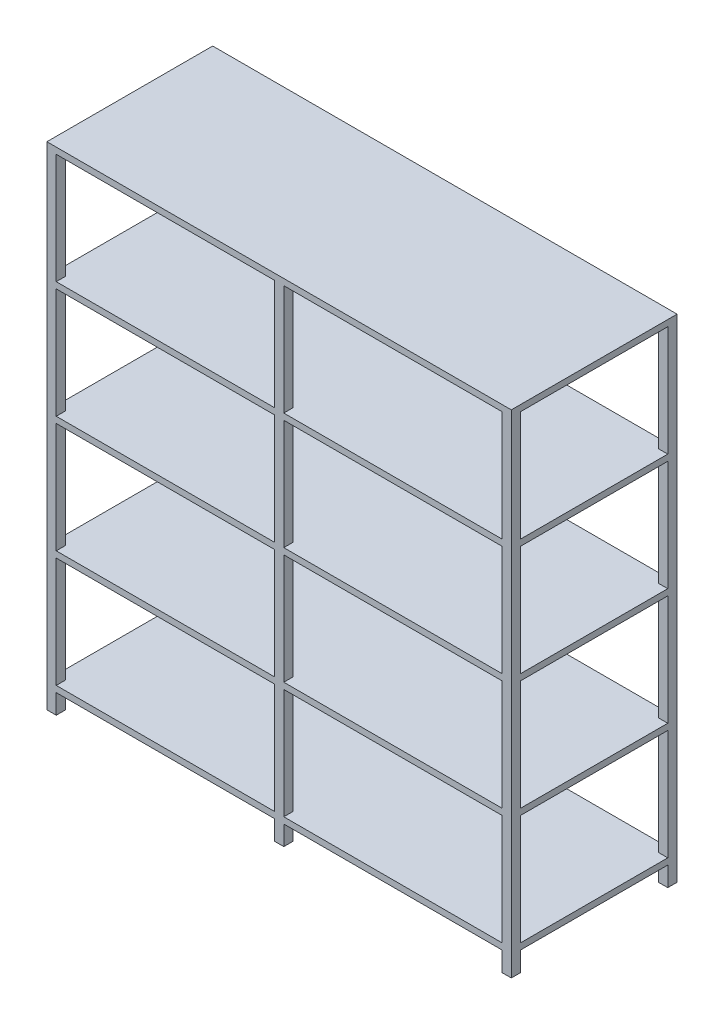
SolidWorks part; units mm, degrees
ref_plane "Alzado" through (0, 0, 0) normal (0, 0, 1) x (1, 0, 0)
ref_plane "Planta" through (0, 0, 0) normal (0, 1, 0) x (1, 0, 0)
ref_plane "Vista lateral" through (0, 0, 0) normal (1, 0, 0) x (0, 0, -1)
sketch "Croquis1" plane through (0, 0, 0) normal (0, 1, 0) x (1, 0, 0)
  line L0 (0, -38.1) -> (0, -338.1) construction
  line L1 (0, 0) -> (38.1, 0)
  line L2 (0, 0) -> (0, -38.1)
  line L3 (0, -38.1) -> (38.1, -38.1)
  line L4 (38.1, 0) -> (38.1, -38.1)
  line L5 (38.1, 0) -> (928.1, 0) construction
  line L6 (966.2, 0) -> (1856.2, 0) construction
  line L7 (928.1, 0) -> (966.2, 0)
  line L8 (928.1, 0) -> (928.1, -38.1)
  line L9 (928.1, -38.1) -> (966.2, -38.1)
  line L10 (966.2, 0) -> (966.2, -38.1)
  line L12 (1856.2, 0) -> (1894.3, 0)
  line L13 (1856.2, 0) -> (1856.2, -38.1)
  line L14 (1856.2, -38.1) -> (1894.3, -38.1)
  line L15 (1894.3, 0) -> (1894.3, -38.1)
  line L16 (0, -338.1) -> (218.5329, -338.1) construction
  line L22 (966.2, -676.2) -> (1856.2, -676.2) construction
  line L23 (38.1, -676.2) -> (928.1, -676.2) construction
  line L28 (1894.3, -676.2) -> (1894.3, -638.1)
  line L29 (1856.2, -638.1) -> (1894.3, -638.1)
  line L30 (1856.2, -676.2) -> (1856.2, -638.1)
  line L31 (1856.2, -676.2) -> (1894.3, -676.2)
  line L32 (966.2, -676.2) -> (966.2, -638.1)
  line L33 (928.1, -638.1) -> (966.2, -638.1)
  line L34 (928.1, -676.2) -> (928.1, -638.1)
  line L35 (928.1, -676.2) -> (966.2, -676.2)
  line L36 (38.1, -676.2) -> (38.1, -638.1)
  line L37 (0, -638.1) -> (38.1, -638.1)
  line L38 (0, -676.2) -> (0, -638.1)
  line L39 (0, -676.2) -> (38.1, -676.2)
  dimension "D1" = 38.1
  dimension "D2" = 38.1
  dimension "D3" = 300
  dimension "D4" = 890
  dimension "D5" = 38.1
  dimension "D6" = 38.1
  dimension "D7" = 890
  dimension "D8" = 38.1
  dimension "D9" = 38.1
extrude "Saliente-Extruir1" add sketch "Croquis1" along normal blind 80
sketch "Croquis2" plane through (0, 80, 0) normal (0, 1, 0) x (1, 0, 0)
  line L1 (0, 0) -> (1894.3, 0)
  line L2 (0, 0) -> (0, -676.2)
  line L3 (0, -676.2) -> (1894.3, -676.2)
  line L4 (1894.3, 0) -> (1894.3, -676.2)
extrude "Saliente-Extruir2" add sketch "Croquis2" along normal blind 25.4
sketch "Croquis3" plane through (0, 105.4, 0) normal (0, 1, 0) x (1, 0, 0)
  line L1 (38.1, -38.1) -> (0, -38.1)
  line L2 (38.1, -38.1) -> (38.1, 0)
  line L3 (38.1, 0) -> (0, 0)
  line L4 (0, -38.1) -> (0, 0)
  line L5 (928.1, 0) -> (966.2, 0)
  line L6 (928.1, 0) -> (928.1, -38.1)
  line L7 (928.1, -38.1) -> (966.2, -38.1)
  line L8 (966.2, 0) -> (966.2, -38.1)
  line L9 (1856.2, 0) -> (1894.3, 0)
  line L10 (1856.2, 0) -> (1856.2, -38.1)
  line L11 (1856.2, -38.1) -> (1894.3, -38.1)
  line L12 (1894.3, 0) -> (1894.3, -38.1)
  line L13 (1856.2, -638.1) -> (1894.3, -638.1)
  line L14 (1856.2, -638.1) -> (1856.2, -676.2)
  line L15 (1856.2, -676.2) -> (1894.3, -676.2)
  line L16 (1894.3, -638.1) -> (1894.3, -676.2)
  line L17 (928.1, -638.1) -> (966.2, -638.1)
  line L18 (928.1, -638.1) -> (928.1, -676.2)
  line L19 (928.1, -676.2) -> (966.2, -676.2)
  line L20 (966.2, -638.1) -> (966.2, -676.2)
  line L21 (0, -638.1) -> (38.1, -638.1)
  line L22 (0, -638.1) -> (0, -676.2)
  line L23 (0, -676.2) -> (38.1, -676.2)
  line L24 (38.1, -638.1) -> (38.1, -676.2)
extrude "Saliente-Extruir3" add sketch "Croquis3" along normal blind 450
sketch "Croquis4" plane through (0, 555.4, 0) normal (0, 1, 0) x (1, 0, 0)
  line L1 (0, 0) -> (1894.3, 0)
  line L2 (0, 0) -> (0, -676.2)
  line L3 (0, -676.2) -> (1894.3, -676.2)
  line L4 (1894.3, 0) -> (1894.3, -676.2)
extrude "Saliente-Extruir4" add sketch "Croquis4" along normal blind 25.4
sketch "Croquis5" plane through (0, 580.8, 0) normal (0, 1, 0) x (1, 0, 0)
  line L1 (38.1, -38.1) -> (0, -38.1)
  line L2 (38.1, -38.1) -> (38.1, 0)
  line L3 (38.1, 0) -> (0, 0)
  line L4 (0, -38.1) -> (0, 0)
  line L5 (928.1, 0) -> (966.2, 0)
  line L6 (928.1, 0) -> (928.1, -38.1)
  line L7 (928.1, -38.1) -> (966.2, -38.1)
  line L8 (966.2, 0) -> (966.2, -38.1)
  line L9 (1856.2, 0) -> (1894.3, 0)
  line L10 (1856.2, 0) -> (1856.2, -38.1)
  line L11 (1856.2, -38.1) -> (1894.3, -38.1)
  line L12 (1894.3, 0) -> (1894.3, -38.1)
  line L13 (1856.2, -638.1) -> (1894.3, -638.1)
  line L14 (1856.2, -638.1) -> (1856.2, -676.2)
  line L15 (1856.2, -676.2) -> (1894.3, -676.2)
  line L16 (1894.3, -638.1) -> (1894.3, -676.2)
  line L17 (928.1, -638.1) -> (966.2, -638.1)
  line L18 (928.1, -638.1) -> (928.1, -676.2)
  line L19 (928.1, -676.2) -> (966.2, -676.2)
  line L20 (966.2, -638.1) -> (966.2, -676.2)
  line L21 (0, -638.1) -> (38.1, -638.1)
  line L22 (0, -638.1) -> (0, -676.2)
  line L23 (0, -676.2) -> (38.1, -676.2)
  line L24 (38.1, -638.1) -> (38.1, -676.2)
extrude "Saliente-Extruir5" add sketch "Croquis5" along normal blind 450
sketch "Croquis6" plane through (0, 1030.8, 0) normal (0, 1, 0) x (1, 0, 0)
  line L1 (0, 0) -> (1894.3, 0)
  line L2 (0, 0) -> (0, -676.2)
  line L3 (0, -676.2) -> (1894.3, -676.2)
  line L4 (1894.3, 0) -> (1894.3, -676.2)
extrude "Saliente-Extruir6" add sketch "Croquis6" along normal blind 25.4
sketch "Croquis7" plane through (0, 1056.2, 0) normal (0, 1, 0) x (1, 0, 0)
  line L1 (38.1, -38.1) -> (0, -38.1)
  line L2 (38.1, -38.1) -> (38.1, 0)
  line L3 (38.1, 0) -> (0, 0)
  line L4 (0, -38.1) -> (0, 0)
  line L5 (928.1, -38.1) -> (966.2, -38.1)
  line L6 (928.1, -38.1) -> (928.1, 0)
  line L7 (928.1, 0) -> (966.2, 0)
  line L8 (966.2, -38.1) -> (966.2, 0)
  line L9 (1856.2, 0) -> (1894.3, 0)
  line L10 (1856.2, 0) -> (1856.2, -38.1)
  line L11 (1856.2, -38.1) -> (1894.3, -38.1)
  line L12 (1894.3, 0) -> (1894.3, -38.1)
  line L13 (1856.2, -638.1) -> (1894.3, -638.1)
  line L14 (1856.2, -638.1) -> (1856.2, -676.2)
  line L15 (1856.2, -676.2) -> (1894.3, -676.2)
  line L16 (1894.3, -638.1) -> (1894.3, -676.2)
  line L17 (928.1, -638.1) -> (966.2, -638.1)
  line L18 (928.1, -638.1) -> (928.1, -676.2)
  line L19 (928.1, -676.2) -> (966.2, -676.2)
  line L20 (966.2, -638.1) -> (966.2, -676.2)
  line L21 (0, -638.1) -> (38.1, -638.1)
  line L22 (0, -638.1) -> (0, -676.2)
  line L23 (0, -676.2) -> (38.1, -676.2)
  line L24 (38.1, -638.1) -> (38.1, -676.2)
extrude "Saliente-Extruir7" add sketch "Croquis7" along normal blind 450
sketch "Croquis8" plane through (0, 1506.2, 0) normal (0, 1, 0) x (1, 0, 0)
  line L1 (0, 0) -> (1894.3, 0)
  line L2 (0, 0) -> (0, -676.2)
  line L3 (0, -676.2) -> (1894.3, -676.2)
  line L4 (1894.3, 0) -> (1894.3, -676.2)
extrude "Saliente-Extruir8" add sketch "Croquis8" along normal blind 25.4
sketch "Croquis9" plane through (0, 1531.6, 0) normal (0, 1, 0) x (1, 0, 0)
  line L1 (0, 0) -> (38.1, 0)
  line L2 (0, 0) -> (0, -38.1)
  line L3 (0, -38.1) -> (38.1, -38.1)
  line L4 (38.1, 0) -> (38.1, -38.1)
  line L5 (928.1, -38.1) -> (966.2, -38.1)
  line L6 (928.1, -38.1) -> (928.1, 0)
  line L7 (928.1, 0) -> (966.2, 0)
  line L8 (966.2, -38.1) -> (966.2, 0)
  line L9 (1856.2, 0) -> (1894.3, 0)
  line L10 (1856.2, 0) -> (1856.2, -38.1)
  line L11 (1856.2, -38.1) -> (1894.3, -38.1)
  line L12 (1894.3, 0) -> (1894.3, -38.1)
  line L13 (1856.2, -676.2) -> (1894.3, -676.2)
  line L14 (1856.2, -676.2) -> (1856.2, -638.1)
  line L15 (1856.2, -638.1) -> (1894.3, -638.1)
  line L16 (1894.3, -676.2) -> (1894.3, -638.1)
  line L17 (928.1, -676.2) -> (966.2, -676.2)
  line L18 (928.1, -676.2) -> (928.1, -638.1)
  line L19 (928.1, -638.1) -> (966.2, -638.1)
  line L20 (966.2, -676.2) -> (966.2, -638.1)
  line L21 (0, -676.2) -> (38.1, -676.2)
  line L22 (0, -676.2) -> (0, -638.1)
  line L23 (0, -638.1) -> (38.1, -638.1)
  line L24 (38.1, -676.2) -> (38.1, -638.1)
extrude "Saliente-Extruir9" add sketch "Croquis9" along normal blind 450
sketch "Croquis10" plane through (0, 1981.6, 0) normal (0, 1, 0) x (1, 0, 0)
  line L1 (0, 0) -> (1894.3, 0)
  line L2 (0, 0) -> (0, -676.2)
  line L3 (0, -676.2) -> (1894.3, -676.2)
  line L4 (1894.3, 0) -> (1894.3, -676.2)
extrude "Saliente-Extruir10" add sketch "Croquis10" along normal blind 25.4
